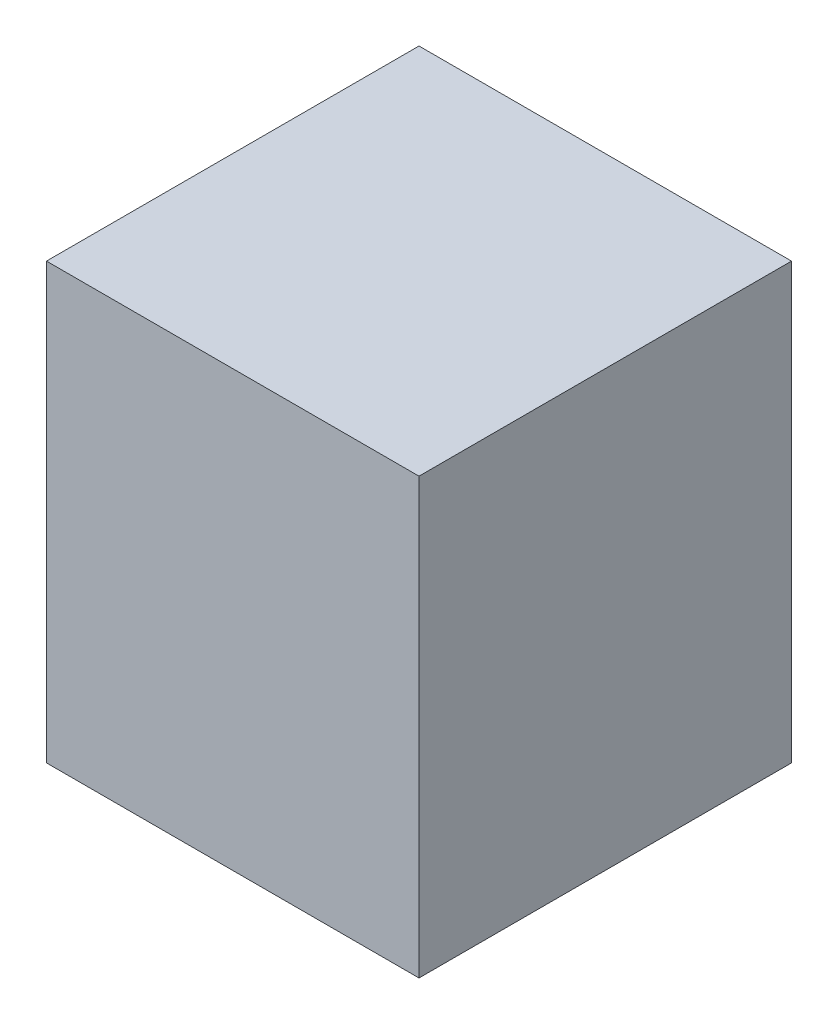
SolidWorks part; units mm, degrees
ref_plane "Front Plane" through (0, 0, 0) normal (0, 0, 1) x (1, 0, 0)
ref_plane "Top Plane" through (0, 0, 0) normal (0, 1, 0) x (1, 0, 0)
ref_plane "Right Plane" through (0, 0, 0) normal (1, 0, 0) x (0, 0, -1)
sketch "Sketch1" plane through (0, 0, 0) normal (0, 0, 1) x (1, 0, 0)
  line L1 (38.1, -44.45) -> (-38.1, -44.45)
  line L2 (38.1, -44.45) -> (38.1, 44.45)
  line L3 (38.1, 44.45) -> (-38.1, 44.45)
  line L4 (-38.1, -44.45) -> (-38.1, 44.45)
  line L5 (38.1, -44.45) -> (-38.1, 44.45) construction
  line L6 (38.1, 44.45) -> (-38.1, -44.45) construction
  point P0 (0, 0)
  dimension "D1" = 76.2
  dimension "D2" = 88.9
extrude "Boss-Extrude1" add sketch "Sketch1" along normal mid plane 76.2
